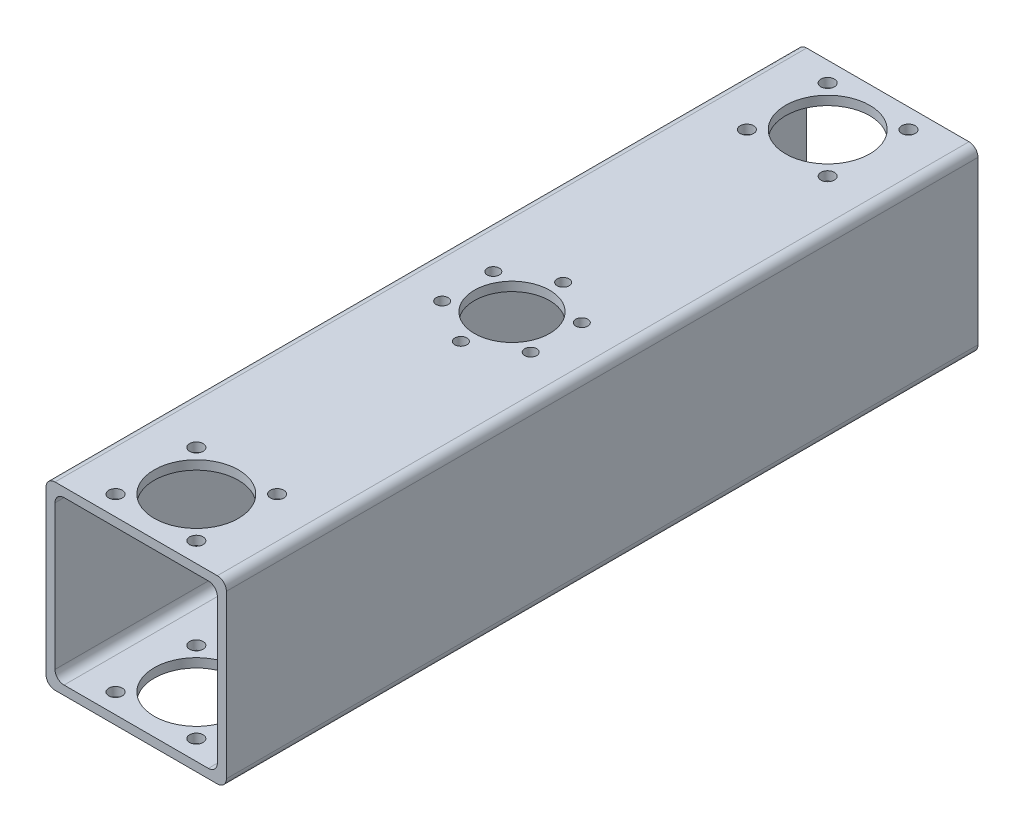
SolidWorks part; units mm, degrees
ref_plane "Płaszczyzna przednia" through (0, 0, 0) normal (0, 0, 1) x (1, 0, 0)
ref_plane "Płaszczyzna górna" through (0, 0, 0) normal (0, 1, 0) x (1, 0, 0)
ref_plane "Płaszczyzna prawa" through (0, 0, 0) normal (1, 0, 0) x (0, 0, -1)
sketch "Sketch1" plane through (0, 0, 0) normal (0, 0, 1) x (1, 0, 0)
  line L1 (-30, 30) -> (30, 30)
  line L2 (-30, 30) -> (-30, -30)
  line L3 (-30, -30) -> (30, -30)
  line L4 (30, 30) -> (30, -30)
  line L5 (-30, 30) -> (30, -30) construction
  line L6 (-30, -30) -> (30, 30) construction
  line L7 (-27, 27) -> (27, 27)
  line L8 (-27, 27) -> (-27, -27)
  line L9 (-27, -27) -> (27, -27)
  line L10 (27, 27) -> (27, -27)
  line L11 (-27, 27) -> (27, -27) construction
  line L12 (-27, -27) -> (27, 27) construction
  point P0 (0, 0)
  point P6 (0, 0)
  dimension "D1" = 60
  dimension "D2" = 60
  dimension "D3" = 54
  dimension "D4" = 54
extrude "Boss-Extrude1" add sketch "Sketch1" along normal blind 250
fillet "Fillet1" radius 3 8 edges at (-27, -27, 125) (27, -27, 125) (27, 27, 125) (-27, 27, 125) (30, -30, 125) (-30, -30, 125) (-30, 30, 125) (30, 30, 125)
sketch "Sketch2" plane through (0, 0, 0) normal (0, 1, 0) x (1, 0, 0)
  line L0 (0, -250) -> (0, 0) construction
  line L1 (27, -250) -> (-27, -250) construction
  line L2 (27, 0) -> (-27, 0) construction
  line L5 (-13.435, -216.565) -> (13.435, -216.565) construction
  line L6 (-13.435, -216.565) -> (-13.435, -243.435) construction
  line L7 (-13.435, -243.435) -> (13.435, -243.435) construction
  line L8 (13.435, -216.565) -> (13.435, -243.435) construction
  line L9 (-13.435, -216.565) -> (13.435, -243.435) construction
  line L10 (-13.435, -243.435) -> (13.435, -216.565) construction
  line L11 (-30, -125) -> (30, -125) construction
  line L12 (-30, -250) -> (-30, 0) construction
  line L13 (30, 0) -> (30, -250) construction
  line L14 (-13.435, -6.565) -> (13.435, -33.435) construction
  line L15 (-13.435, -33.435) -> (13.435, -6.565) construction
  line L16 (13.435, -33.435) -> (13.435, -6.565) construction
  line L17 (-13.435, -6.565) -> (13.435, -6.565) construction
  line L18 (-13.435, -33.435) -> (-13.435, -6.565) construction
  line L19 (-13.435, -33.435) -> (13.435, -33.435) construction
  circle A1 centre (0, -125) radius 17 construction
  circle A2 centre (0, -142) radius 2
  circle A3 centre (-14.7224, -133.5) radius 2
  circle A4 centre (-14.7224, -116.5) radius 2
  circle A5 centre (0, -108) radius 2
  circle A6 centre (14.7224, -116.5) radius 2
  circle A7 centre (14.7224, -133.5) radius 2
  circle A8 centre (-13.435, -216.565) radius 2.25
  circle A9 centre (13.435, -216.565) radius 2.25
  circle A10 centre (13.435, -243.435) radius 2.25
  circle A11 centre (-13.435, -243.435) radius 2.25
  circle A12 centre (-13.435, -6.565) radius 2.25
  circle A13 centre (13.435, -6.565) radius 2.25
  circle A14 centre (13.435, -33.435) radius 2.25
  circle A15 centre (-13.435, -33.435) radius 2.25
  circle A16 centre (0, -125) radius 12.5
  circle A17 centre (0, -230) radius 14
  circle A18 centre (0, -20) radius 14
  point P13 (0, -230)
  point P24 (0, -125)
  point P45 (0, -20)
  dimension "D2" = 34
  dimension "D3" = 4
  dimension "D8" = 4.5
  dimension "D9" = 25
  dimension "D10" = 28
  dimension "D1" = 125
  dimension "D5" = 38
  dimension "D7" = 20
  dimension "D4" = 6
extrude "Cut-Extrude1" cut sketch "Sketch2" along normal through all and the other way through all
